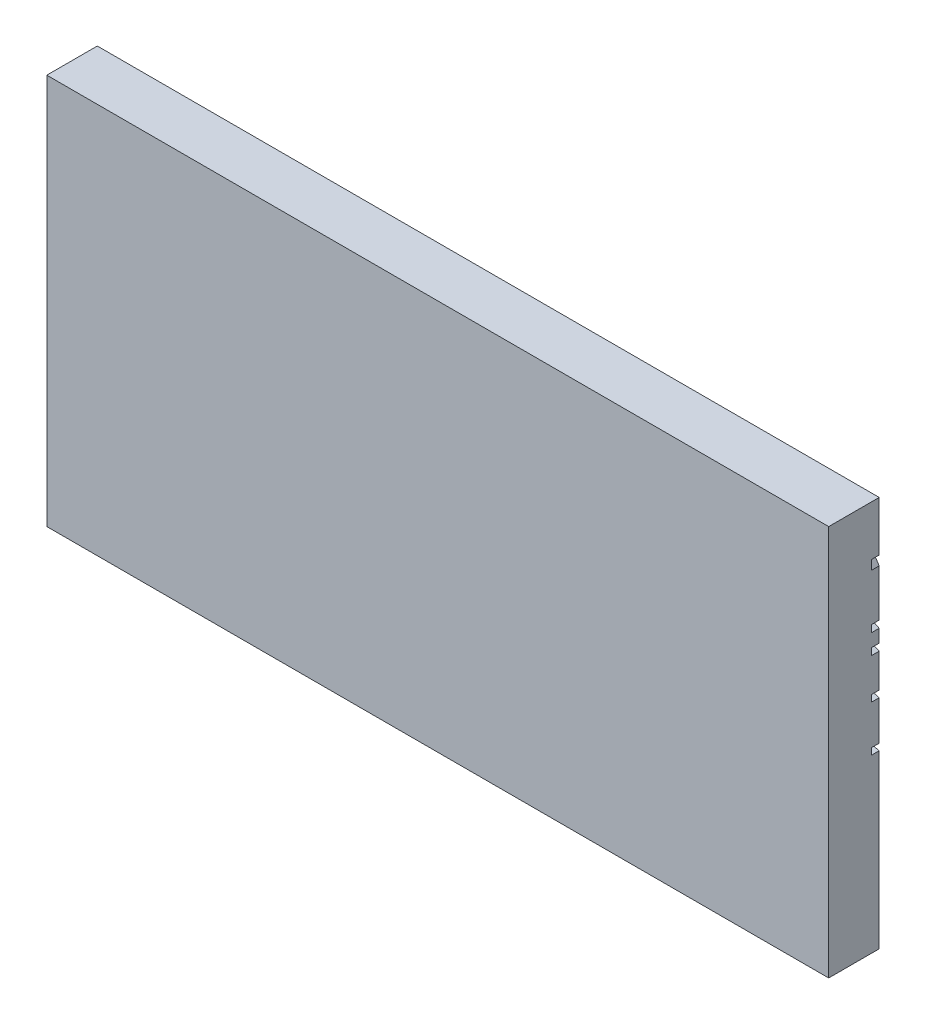
SolidWorks part; units mm, degrees
ref_plane "Front Plane" through (0, 0, 0) normal (0, 0, 1) x (1, 0, 0)
ref_plane "Top Plane" through (0, 0, 0) normal (0, 1, 0) x (1, 0, 0)
ref_plane "Right Plane" through (0, 0, 0) normal (1, 0, 0) x (0, 0, -1)
sketch "Sketch1" plane through (0, 0, 0) normal (0, 0, 1) x (1, 0, 0)
  line L1 (-99.5775, 43.7213) -> (52.8225, 43.7213)
  line L2 (-99.5775, 43.7213) -> (-99.5775, -32.4787)
  line L3 (-99.5775, -32.4787) -> (52.8225, -32.4787)
  line L4 (52.8225, 43.7213) -> (52.8225, -32.4787)
  dimension "D1" = 152.4
  dimension "D2" = 76.2
extrude "Boss-Extrude1" add sketch "Sketch1" along normal blind 9.8425
sketch "Sketch3" plane through (0, 0, 0) normal (0, 0, -1) x (-1, 0, 0)
  line L0 (-44.7269, 19.3653) -> (-44.7462, 20.6051)
  line L1 (-48.5104, 12.3383) -> (-54.6406, 10.7146)
  line L2 (-43.6958, 23.0575) -> (-43.5857, 24.2926)
  line L3 (-50.9274, 36.9001) -> (-54.9444, 30.744)
  line L4 (-50.3182, 37.5949) -> (-48.8353, 39.2334)
  line L5 (-49.5767, 36.9238) -> (-48.0938, 38.5624)
  line L6 (-50.0613, 36.3975) -> (-54.9444, 28.9141)
  line L7 (-48.0938, 38.5624) -> (-48.8353, 39.2334)
  line L8 (-54.9444, 30.744) -> (-54.9444, 28.9141)
  line L9 (-49.73, 24.4824) -> (-54.8745, 22.0346)
  line L10 (-48.611, 24.7405) -> (-43.5857, 24.2926)
  line L11 (-49.1972, 23.3627) -> (-54.8745, 20.6614)
  line L12 (-48.7211, 23.5054) -> (-43.6958, 23.0575)
  line L13 (-50.2037, 20.2853) -> (-54.9699, 18.1742)
  line L14 (-48.5082, 20.5466) -> (-44.7462, 20.6051)
  line L15 (-49.7015, 19.1515) -> (-54.9699, 16.818)
  line L16 (-48.4889, 19.3068) -> (-44.7269, 19.3653)
  line L17 (-54.8745, 22.0346) -> (-54.8745, 20.6614)
  line L18 (-54.9699, 18.1742) -> (-54.9699, 16.818)
  line L19 (-46.9187, 12.5019) -> (-44.7269, 12.3833)
  line L20 (-48.1929, 11.1397) -> (-54.3231, 9.5159)
  line L21 (-46.9857, 11.2637) -> (-44.7939, 11.1451)
  line L22 (-44.7939, 11.1451) -> (-44.7269, 12.3833)
  line L23 (-54.3231, 9.5159) -> (-54.6406, 10.7146)
  line L24 (-46.9964, 3.6185) -> (-54.8645, 1.7475)
  line L25 (-46.1288, 3.7035) -> (-43.5857, 3.6071)
  line L26 (-46.7095, 2.4122) -> (-54.5776, 0.5411)
  line L27 (-46.1758, 2.4644) -> (-43.6327, 2.368)
  line L28 (-43.6327, 2.368) -> (-43.5857, 3.6071)
  line L29 (-54.8645, 1.7475) -> (-54.5776, 0.5411)
  spline S0 degree 3 poles (-46.9187, 12.5019) (-47.1944, 12.5168) (-47.7292, 12.5032) (-48.2553, 12.4059) (-48.5104, 12.3383) knots 0 0 0 0 0.51111 1 1 1 1
  spline S1 degree 3 poles (-48.1929, 11.1397) (-47.8018, 11.2432) (-47.3896, 11.2855) (-46.9857, 11.2637) knots 0 0 0 0 1 1 1 1
  spline S2 degree 3 poles (-50.3182, 37.5949) (-50.3856, 37.5204) (-50.6094, 37.3056) (-50.8312, 37.088) (-50.9274, 36.9001) knots 0 0 0 0 0.326998 1 1 1 1
  spline S3 degree 3 poles (-49.5767, 36.9238) (-49.6461, 36.8472) (-49.8093, 36.6862) (-49.9597, 36.5415) (-50.0196, 36.4739) (-50.0397, 36.4395) (-50.0306, 36.4576) (-50.0534, 36.413) (-50.0613, 36.3975) knots 0 0 0 0 0.263904 0.527807 0.791711 0.923663 0.989639 1.055615 1.055615 1.055615 1.055615
  spline S4 degree 3 poles (-49.73, 24.4824) (-49.6594, 24.5159) (-49.4464, 24.611) (-49.0756, 24.7307) (-48.7671, 24.7545) (-48.611, 24.7405) knots 0 0 0 0 0.202889 0.601788 1 1 1 1
  spline S5 degree 3 poles (-49.1972, 23.3627) (-49.139, 23.3903) (-49.011, 23.4462) (-48.8722, 23.4903) (-48.7687, 23.5072) (-48.7402, 23.5071) (-48.7211, 23.5054) knots 0 0 0 0 0.25 0.5 0.75 1 1 1 1
  spline S6 degree 3 poles (-48.5082, 20.5466) (-48.6759, 20.544) (-48.9996, 20.5089) (-49.4534, 20.4731) (-49.8713, 20.4107) (-50.0809, 20.3397) (-50.2037, 20.2853) knots 0 0 0 0 0.29409 0.560497 0.802762 1 1 1 1
  spline S7 degree 3 poles (-49.7015, 19.1515) (-49.6842, 19.1592) (-49.6419, 19.1767) (-49.6151, 19.1855) (-49.5423, 19.2057) (-49.306, 19.2391) (-49.0487, 19.2616) (-48.8141, 19.2833) (-48.6177, 19.3016) (-48.536, 19.306) (-48.4889, 19.3068) knots 0 0 0 0 0.0625 0.125 0.25 0.5 0.625 0.75 0.875 1 1 1 1
  spline S8 degree 3 poles (-46.1288, 3.7035) (-46.2914, 3.7097) (-46.5824, 3.6989) (-46.8693, 3.6487) (-46.9964, 3.6185) knots 0 0 0 0 0.554289 1 1 1 1
  spline S9 degree 1 poles (-46.1758, 2.4644) (-46.7095, 2.4122) knots 0 0 1 1 construction
  spline S10 degree 3 poles (-46.7095, 2.4122) (-46.5356, 2.4535) (-46.3544, 2.4712) (-46.1758, 2.4644) knots 0 0 0 0 1 1 1 1
  dimension "D1" = 0.928
  dimension "D2" = 1.1624
  dimension "D3" = 1.7244
  dimension "D4" = 1.6066
  dimension "D5" = 1.24
extrude "Cut-Extrude8" cut sketch "Sketch3" against normal blind 1.5 contours L3 L8 L6 S3 L5 L7 L4 S2 | L10 L2 L12 S5 L11 L17 L9 S4 | L14 L0 L16 S7 L15 L18 L13 S6 | L19 L22 L21 S1 L20 L23 L1 S0 | L25 L28 L27 S10 L26 L29 L24 S8
